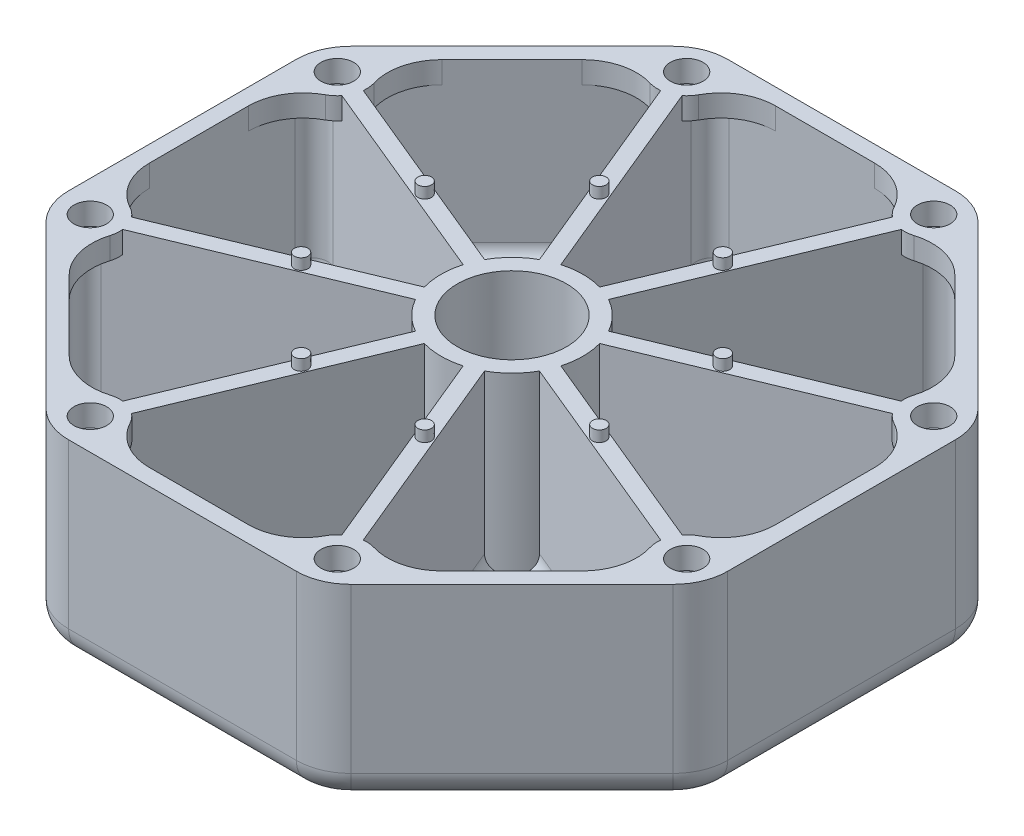
SolidWorks part; units mm, degrees
ref_plane "Front Plane" through (0, 0, 0) normal (0, 0, 1) x (1, 0, 0)
ref_plane "Top Plane" through (0, 0, 0) normal (0, 1, 0) x (1, 0, 0)
ref_plane "Right Plane" through (0, 0, 0) normal (1, 0, 0) x (0, 0, -1)
sketch "Sketch1" plane through (0, 0, 0) normal (0, 1, 0) x (1, 0, 0)
  line L9 (27.9289, -57.4264) -> (57.4264, -27.9289)
  line L10 (60.3553, -20.8579) -> (60.3553, 20.8579)
  line L11 (57.4264, 27.9289) -> (27.9289, 57.4264)
  line L12 (20.8579, 60.3553) -> (-20.8579, 60.3553)
  line L13 (-27.9289, 57.4264) -> (-57.4264, 27.9289)
  line L14 (-60.3553, 20.8579) -> (-60.3553, -20.8579)
  line L15 (-57.4264, -27.9289) -> (-27.9289, -57.4264)
  line L16 (-20.8579, -60.3553) -> (20.8579, -60.3553)
  circle A0 centre (0, 0) radius 60.3553 construction
  arc A9 (-20.8579, 60.3553) -> (-27.9289, 57.4264) centre (-20.8579, 50.3553) ccw
  arc A10 (27.9289, 57.4264) -> (20.8579, 60.3553) centre (20.8579, 50.3553) ccw
  arc A11 (60.3553, 20.8579) -> (57.4264, 27.9289) centre (50.3553, 20.8579) ccw
  arc A12 (57.4264, -27.9289) -> (60.3553, -20.8579) centre (50.3553, -20.8579) ccw
  arc A13 (27.9289, -57.4264) -> (20.8579, -60.3553) centre (20.8579, -50.3553) cw
  arc A14 (-27.9289, -57.4264) -> (-20.8579, -60.3553) centre (-20.8579, -50.3553) ccw
  arc A15 (-60.3553, -20.8579) -> (-57.4264, -27.9289) centre (-50.3553, -20.8579) ccw
  arc A16 (-57.4264, 27.9289) -> (-60.3553, 20.8579) centre (-50.3553, 20.8579) ccw
  point P18 (60.3553, -25)
  point P21 (25, -60.3553)
  dimension "D1" = 50
  dimension "D2" = 10
extrude "Boss-Extrude1" add sketch "Sketch1" along normal blind 3
sketch "Sketch2" plane through (0, 3, 0) normal (0, 1, 0) x (1, 0, 0)
  line L0 (28.0802, -53.0325) -> (53.0325, -28.0802)
  line L1 (57.3553, -17.644) -> (57.3553, 17.644)
  line L2 (53.0325, 28.0802) -> (28.0802, 53.0325)
  line L3 (17.644, 57.3553) -> (-17.644, 57.3553)
  line L4 (-28.0802, 53.0325) -> (-53.0325, 28.0802)
  line L5 (-57.3553, 17.644) -> (-57.3553, -17.644)
  line L6 (-53.0325, -28.0802) -> (-28.0802, -53.0325)
  line L7 (-17.644, -57.3553) -> (17.644, -57.3553)
  line L8 (27.9289, -57.4264) -> (57.4264, -27.9289)
  line L9 (60.3553, -20.8579) -> (60.3553, 20.8579)
  line L10 (57.4264, 27.9289) -> (27.9289, 57.4264)
  line L11 (20.8579, 60.3553) -> (-20.8579, 60.3553)
  line L12 (-27.9289, 57.4264) -> (-57.4264, 27.9289)
  line L13 (-60.3553, 20.8579) -> (-60.3553, -20.8579)
  line L14 (-57.4264, -27.9289) -> (-27.9289, -57.4264)
  line L15 (-20.8579, -60.3553) -> (20.8579, -60.3553)
  line L16 (27.9289, -57.4264) -> (57.4264, -27.9289)
  line L17 (60.3553, -20.8579) -> (60.3553, 20.8579)
  line L18 (57.4264, 27.9289) -> (27.9289, 57.4264)
  line L19 (20.8579, 60.3553) -> (-20.8579, 60.3553)
  line L20 (-27.9289, 57.4264) -> (-57.4264, 27.9289)
  line L21 (-60.3553, 20.8579) -> (-60.3553, -20.8579)
  line L22 (-57.4264, -27.9289) -> (-27.9289, -57.4264)
  line L23 (-20.8579, -60.3553) -> (20.8579, -60.3553)
  line L24 (0, 0) -> (-20.8579, -50.3553) construction
  line L25 (-20.8579, -50.3553) -> (-29.9913, -72.4054) construction
  line L26 (-20.4156, -53.2073) -> (-3.5558, -12.5042)
  line L27 (-23.1872, -52.0592) -> (-6.3275, -11.3562)
  line L28 (-55.3051, -25.8076) -> (-25.8076, -55.3051) construction
  line L29 (-20.8579, -57.3553) -> (20.8579, -57.3553) construction
  line L30 (-52.0592, -23.1872) -> (-11.3562, -6.3275)
  line L31 (-53.2073, -20.4156) -> (-12.5042, -3.5558)
  line L32 (-53.2073, 20.4156) -> (-12.5042, 3.5558)
  line L33 (-52.0592, 23.1872) -> (-11.3562, 6.3275)
  line L34 (-23.1872, 52.0592) -> (-6.3275, 11.3562)
  line L35 (-20.4156, 53.2073) -> (-3.5558, 12.5042)
  line L36 (20.4156, 53.2073) -> (3.5558, 12.5042)
  line L37 (23.1872, 52.0592) -> (6.3275, 11.3562)
  line L38 (52.0592, 23.1872) -> (11.3562, 6.3275)
  line L39 (53.2073, 20.4156) -> (12.5042, 3.5558)
  line L40 (53.2073, -20.4156) -> (12.5042, -3.5558)
  line L41 (52.0592, -23.1872) -> (11.3562, -6.3275)
  line L42 (23.1872, -52.0592) -> (6.3275, -11.3562)
  line L43 (20.4156, -53.2073) -> (3.5558, -12.5042)
  line L44 (-57.3553, 20.8579) -> (-57.3553, -20.8579) construction
  line L45 (-25.8076, 55.3051) -> (-55.3051, 25.8076) construction
  line L46 (20.8579, 57.3553) -> (-20.8579, 57.3553) construction
  line L47 (55.3051, 25.8076) -> (25.8076, 55.3051) construction
  line L48 (57.3553, -20.8579) -> (57.3553, 20.8579) construction
  line L49 (25.8076, -55.3051) -> (55.3051, -25.8076) construction
  arc A8 (57.4264, -27.9289) -> (60.3553, -20.8579) centre (50.3553, -20.8579) ccw
  arc A9 (60.3553, 20.8579) -> (57.4264, 27.9289) centre (50.3553, 20.8579) ccw
  arc A10 (27.9289, 57.4264) -> (20.8579, 60.3553) centre (20.8579, 50.3553) ccw
  arc A11 (-20.8579, 60.3553) -> (-27.9289, 57.4264) centre (-20.8579, 50.3553) ccw
  arc A12 (-57.4264, 27.9289) -> (-60.3553, 20.8579) centre (-50.3553, 20.8579) ccw
  arc A13 (-60.3553, -20.8579) -> (-57.4264, -27.9289) centre (-50.3553, -20.8579) ccw
  arc A14 (-27.9289, -57.4264) -> (-20.8579, -60.3553) centre (-20.8579, -50.3553) ccw
  arc A15 (20.8579, -60.3553) -> (27.9289, -57.4264) centre (20.8579, -50.3553) ccw
  arc A16 (57.4264, -27.9289) -> (60.3553, -20.8579) centre (50.3553, -20.8579) ccw
  arc A17 (60.3553, 20.8579) -> (57.4264, 27.9289) centre (50.3553, 20.8579) ccw
  arc A18 (27.9289, 57.4264) -> (20.8579, 60.3553) centre (20.8579, 50.3553) ccw
  arc A19 (-20.8579, 60.3553) -> (-27.9289, 57.4264) centre (-20.8579, 50.3553) ccw
  arc A20 (-57.4264, 27.9289) -> (-60.3553, 20.8579) centre (-50.3553, 20.8579) ccw
  arc A21 (-60.3553, -20.8579) -> (-57.4264, -27.9289) centre (-50.3553, -20.8579) ccw
  arc A22 (-27.9289, -57.4264) -> (-20.8579, -60.3553) centre (-20.8579, -50.3553) ccw
  arc A23 (20.8579, -60.3553) -> (27.9289, -57.4264) centre (20.8579, -50.3553) ccw
  circle A24 centre (0, 0) radius 10
  arc A25 (-11.3562, -6.3275) -> (-6.3275, -11.3562) centre (0, 0) ccw
  arc A26 (-23.1872, -52.0592) -> (-28.0802, -53.0325) centre (-25.9589, -50.9112) cw
  arc A27 (-17.644, -57.3553) -> (-20.4156, -53.2073) centre (-17.644, -54.3553) cw
  arc A28 (-25.8076, -55.3051) -> (-20.8579, -57.3553) centre (-20.8579, -50.3553) ccw construction
  arc A29 (-53.2073, -20.4156) -> (-57.3553, -17.644) centre (-54.3553, -17.644) cw
  arc A30 (-53.0325, -28.0802) -> (-52.0592, -23.1872) centre (-50.9112, -25.9589) cw
  arc A31 (-52.0592, 23.1872) -> (-53.0325, 28.0802) centre (-50.9112, 25.9589) cw
  arc A32 (-57.3553, 17.644) -> (-53.2073, 20.4156) centre (-54.3553, 17.644) cw
  arc A33 (-20.4156, 53.2073) -> (-17.644, 57.3553) centre (-17.644, 54.3553) cw
  arc A34 (-28.0802, 53.0325) -> (-23.1872, 52.0592) centre (-25.9589, 50.9112) cw
  arc A35 (23.1872, 52.0592) -> (28.0802, 53.0325) centre (25.9589, 50.9112) cw
  arc A36 (17.644, 57.3553) -> (20.4156, 53.2073) centre (17.644, 54.3553) cw
  arc A37 (53.2073, 20.4156) -> (57.3553, 17.644) centre (54.3553, 17.644) cw
  arc A38 (53.0325, 28.0802) -> (52.0592, 23.1872) centre (50.9112, 25.9589) cw
  arc A39 (52.0592, -23.1872) -> (53.0325, -28.0802) centre (50.9112, -25.9589) cw
  arc A40 (57.3553, -17.644) -> (53.2073, -20.4156) centre (54.3553, -17.644) cw
  arc A41 (20.4156, -53.2073) -> (17.644, -57.3553) centre (17.644, -54.3553) cw
  arc A42 (28.0802, -53.0325) -> (23.1872, -52.0592) centre (25.9589, -50.9112) cw
  arc A43 (-57.3553, -20.8579) -> (-55.3051, -25.8076) centre (-50.3553, -20.8579) ccw construction
  arc A44 (-55.3051, 25.8076) -> (-57.3553, 20.8579) centre (-50.3553, 20.8579) ccw construction
  arc A45 (-20.8579, 57.3553) -> (-25.8076, 55.3051) centre (-20.8579, 50.3553) ccw construction
  arc A46 (25.8076, 55.3051) -> (20.8579, 57.3553) centre (20.8579, 50.3553) ccw construction
  arc A47 (57.3553, 20.8579) -> (55.3051, 25.8076) centre (50.3553, 20.8579) ccw construction
  arc A48 (55.3051, -25.8076) -> (57.3553, -20.8579) centre (50.3553, -20.8579) ccw construction
  arc A49 (20.8579, -57.3553) -> (25.8076, -55.3051) centre (20.8579, -50.3553) ccw construction
  circle A50 centre (0, 0) radius 13 construction
  arc A51 (-12.5042, 3.5558) -> (-12.5042, -3.5558) centre (0, 0) ccw
  arc A52 (-6.3275, 11.3562) -> (-11.3562, 6.3275) centre (0, 0) ccw
  arc A53 (3.5558, 12.5042) -> (-3.5558, 12.5042) centre (0, 0) ccw
  arc A54 (11.3562, 6.3275) -> (6.3275, 11.3562) centre (0, 0) ccw
  arc A55 (12.5042, -3.5558) -> (12.5042, 3.5558) centre (0, 0) ccw
  arc A56 (6.3275, -11.3562) -> (11.3562, -6.3275) centre (0, 0) ccw
  arc A57 (-3.5558, -12.5042) -> (3.5558, -12.5042) centre (0, 0) ccw
  point P121 (0, 0)
  dimension "D3" = 20
  dimension "D7" = 3
  dimension "D5" = 1.5
  dimension "D6" = 1.5
  dimension "D1" = 0
  dimension "D2" = 3
  dimension "D4" = 3
extrude "Boss-Extrude2" add sketch "Sketch2" along normal blind 28
sketch "Sketch3" plane through (0, 31, 0) normal (0, 1, 0) x (1, 0, 0)
  line L0 (-20.2449, -52.7952) -> (-20.4156, -53.2073)
  line L1 (50.4221, 19.2619) -> (12.5042, 3.5558)
  line L2 (19.2619, -50.4221) -> (3.5558, -12.5042)
  line L3 (-53.0325, -28.0802) -> (-28.0802, -53.0325)
  line L4 (-23.1872, -52.0592) -> (-6.3275, -11.3562)
  line L5 (-11.3562, -6.3275) -> (-52.0592, -23.1872)
  line L6 (-46.9695, -34.1432) -> (-34.1432, -46.9695)
  line L7 (-22.0336, -49.2741) -> (-6.3275, -11.3562)
  line L8 (-20.8579, -60.3553) -> (20.8579, -60.3553)
  line L9 (27.9289, -57.4264) -> (57.4264, -27.9289)
  line L10 (60.3553, -20.8579) -> (60.3553, 20.8579)
  line L11 (57.4264, 27.9289) -> (27.9289, 57.4264)
  line L12 (20.8579, 60.3553) -> (-20.8579, 60.3553)
  line L13 (-27.9289, 57.4264) -> (-57.4264, 27.9289)
  line L14 (-60.3553, 20.8579) -> (-60.3553, -20.8579)
  line L15 (-57.4264, -27.9289) -> (-27.9289, -57.4264)
  line L16 (-20.8579, -60.3553) -> (20.8579, -60.3553)
  line L17 (27.9289, -57.4264) -> (57.4264, -27.9289)
  line L18 (60.3553, -20.8579) -> (60.3553, 20.8579)
  line L19 (57.4264, 27.9289) -> (27.9289, 57.4264)
  line L20 (20.8579, 60.3553) -> (-20.8579, 60.3553)
  line L21 (-27.9289, 57.4264) -> (-57.4264, 27.9289)
  line L22 (-60.3553, 20.8579) -> (-60.3553, -20.8579)
  line L23 (-57.4264, -27.9289) -> (-27.9289, -57.4264)
  line L24 (-11.3562, -6.3275) -> (-49.2741, -22.0336)
  line L25 (-12.5042, 3.5558) -> (-53.2073, 20.4156)
  line L26 (-53.2073, -20.4156) -> (-12.5042, -3.5558)
  line L27 (-57.3553, 17.644) -> (-57.3553, -17.644)
  line L28 (-12.5042, 3.5558) -> (-50.4221, 19.2619)
  line L30 (-57.3553, 9.0696) -> (-57.3553, -9.0696)
  line L31 (-28.0802, 53.0325) -> (-53.0325, 28.0802)
  line L32 (-52.0592, 23.1872) -> (-11.3562, 6.3275)
  line L33 (-6.3275, 11.3562) -> (-23.1872, 52.0592)
  line L34 (-34.1432, 46.9695) -> (-46.9695, 34.1432)
  line L35 (-49.2741, 22.0336) -> (-11.3562, 6.3275)
  line L36 (-6.3275, 11.3562) -> (-22.0336, 49.2741)
  line L37 (3.5558, 12.5042) -> (20.4156, 53.2073)
  line L38 (-20.4156, 53.2073) -> (-3.5558, 12.5042)
  line L39 (17.644, 57.3553) -> (-17.644, 57.3553)
  line L40 (3.5558, 12.5042) -> (19.2619, 50.4221)
  line L42 (9.0696, 57.3553) -> (-9.0696, 57.3553)
  line L43 (53.0325, 28.0802) -> (28.0802, 53.0325)
  line L44 (23.1872, 52.0592) -> (6.3275, 11.3562)
  line L45 (11.3562, 6.3275) -> (52.0592, 23.1872)
  line L46 (46.9695, 34.1432) -> (34.1432, 46.9695)
  line L48 (11.3562, 6.3275) -> (49.2741, 22.0336)
  line L49 (12.5042, -3.5558) -> (53.2073, -20.4156)
  line L50 (53.2073, 20.4156) -> (12.5042, 3.5558)
  line L51 (57.3553, -17.644) -> (57.3553, 17.644)
  line L52 (12.5042, -3.5558) -> (50.4221, -19.2619)
  line L54 (57.3553, -9.0696) -> (57.3553, 9.0696)
  line L55 (-17.644, -57.3553) -> (17.644, -57.3553)
  line L56 (-3.5558, -12.5042) -> (-20.4156, -53.2073)
  line L57 (20.4156, -53.2073) -> (3.5558, -12.5042)
  line L58 (-9.0696, -57.3553) -> (9.0696, -57.3553)
  line L59 (-3.5558, -12.5042) -> (-19.2619, -50.4221)
  line L61 (28.0802, -53.0325) -> (53.0325, -28.0802)
  line L62 (52.0592, -23.1872) -> (11.3562, -6.3275)
  line L63 (6.3275, -11.3562) -> (23.1872, -52.0592)
  line L64 (34.1432, -46.9695) -> (46.9695, -34.1432)
  line L66 (6.3275, -11.3562) -> (22.0336, -49.2741)
  line L67 (49.2741, -22.0336) -> (11.3562, -6.3275)
  line L68 (22.0336, 49.2741) -> (6.3275, 11.3562)
  line L69 (-19.2619, 50.4221) -> (-3.5558, 12.5042)
  line L70 (-50.4221, -19.2619) -> (-12.5042, -3.5558)
  circle A1 centre (0, 0) radius 10
  circle A2 centre (0, 0) radius 10
  circle A3 centre (-22.6249, -54.6215) radius 3
  arc A5 (-28.0802, -53.0325) -> (-23.1872, -52.0592) centre (-25.9589, -50.9112) ccw
  arc A6 (-11.3562, -6.3275) -> (-6.3275, -11.3562) centre (0, 0) ccw
  arc A7 (-52.0592, -23.1872) -> (-53.0325, -28.0802) centre (-50.9112, -25.9589) ccw
  arc A8 (20.8579, -60.3553) -> (27.9289, -57.4264) centre (20.8579, -50.3553) ccw
  arc A9 (57.4264, -27.9289) -> (60.3553, -20.8579) centre (50.3553, -20.8579) ccw
  arc A10 (60.3553, 20.8579) -> (57.4264, 27.9289) centre (50.3553, 20.8579) ccw
  arc A11 (27.9289, 57.4264) -> (20.8579, 60.3553) centre (20.8579, 50.3553) ccw
  arc A12 (-20.8579, 60.3553) -> (-27.9289, 57.4264) centre (-20.8579, 50.3553) ccw
  arc A13 (-57.4264, 27.9289) -> (-60.3553, 20.8579) centre (-50.3553, 20.8579) ccw
  arc A14 (-60.3553, -20.8579) -> (-57.4264, -27.9289) centre (-50.3553, -20.8579) ccw
  arc A15 (-27.9289, -57.4264) -> (-20.8579, -60.3553) centre (-20.8579, -50.3553) ccw
  arc A16 (20.8579, -60.3553) -> (27.9289, -57.4264) centre (20.8579, -50.3553) ccw
  arc A17 (57.4264, -27.9289) -> (60.3553, -20.8579) centre (50.3553, -20.8579) ccw
  arc A18 (60.3553, 20.8579) -> (57.4264, 27.9289) centre (50.3553, 20.8579) ccw
  arc A19 (27.9289, 57.4264) -> (20.8579, 60.3553) centre (20.8579, 50.3553) ccw
  arc A20 (-20.8579, 60.3553) -> (-27.9289, 57.4264) centre (-20.8579, 50.3553) ccw
  arc A21 (-57.4264, 27.9289) -> (-60.3553, 20.8579) centre (-50.3553, 20.8579) ccw
  arc A22 (-60.3553, -20.8579) -> (-57.4264, -27.9289) centre (-50.3553, -20.8579) ccw
  arc A23 (-27.9289, -57.4264) -> (-20.8579, -60.3553) centre (-20.8579, -50.3553) ccw
  arc A25 (-11.3562, -6.3275) -> (-6.3275, -11.3562) centre (0, 0) ccw
  arc A27 (-12.5042, 3.5558) -> (-12.5042, -3.5558) centre (0, 0) ccw
  arc A28 (-57.3553, -17.644) -> (-53.2073, -20.4156) centre (-54.3553, -17.644) ccw
  arc A29 (-53.2073, 20.4156) -> (-57.3553, 17.644) centre (-54.3553, 17.644) ccw
  arc A30 (-12.5042, 3.5558) -> (-12.5042, -3.5558) centre (0, 0) ccw
  arc A33 (-53.0325, 28.0802) -> (-52.0592, 23.1872) centre (-50.9112, 25.9589) ccw
  arc A34 (-6.3275, 11.3562) -> (-11.3562, 6.3275) centre (0, 0) ccw
  arc A35 (-23.1872, 52.0592) -> (-28.0802, 53.0325) centre (-25.9589, 50.9112) ccw
  arc A37 (-6.3275, 11.3562) -> (-11.3562, 6.3275) centre (0, 0) ccw
  arc A39 (3.5558, 12.5042) -> (-3.5558, 12.5042) centre (0, 0) ccw
  arc A40 (-17.644, 57.3553) -> (-20.4156, 53.2073) centre (-17.644, 54.3553) ccw
  arc A41 (20.4156, 53.2073) -> (17.644, 57.3553) centre (17.644, 54.3553) ccw
  arc A42 (3.5558, 12.5042) -> (-3.5558, 12.5042) centre (0, 0) ccw
  arc A45 (28.0802, 53.0325) -> (23.1872, 52.0592) centre (25.9589, 50.9112) ccw
  arc A46 (11.3562, 6.3275) -> (6.3275, 11.3562) centre (0, 0) ccw
  arc A47 (52.0592, 23.1872) -> (53.0325, 28.0802) centre (50.9112, 25.9589) ccw
  arc A49 (11.3562, 6.3275) -> (6.3275, 11.3562) centre (0, 0) ccw
  arc A51 (12.5042, -3.5558) -> (12.5042, 3.5558) centre (0, 0) ccw
  arc A52 (57.3553, 17.644) -> (53.2073, 20.4156) centre (54.3553, 17.644) ccw
  arc A53 (53.2073, -20.4156) -> (57.3553, -17.644) centre (54.3553, -17.644) ccw
  arc A54 (12.5042, -3.5558) -> (12.5042, 3.5558) centre (0, 0) ccw
  arc A57 (-20.4156, -53.2073) -> (-17.644, -57.3553) centre (-17.644, -54.3553) ccw
  arc A58 (-3.5558, -12.5042) -> (3.5558, -12.5042) centre (0, 0) ccw
  arc A59 (17.644, -57.3553) -> (20.4156, -53.2073) centre (17.644, -54.3553) ccw
  arc A61 (-3.5558, -12.5042) -> (3.5558, -12.5042) centre (0, 0) ccw
  arc A63 (53.0325, -28.0802) -> (52.0592, -23.1872) centre (50.9112, -25.9589) ccw
  arc A64 (6.3275, -11.3562) -> (11.3562, -6.3275) centre (0, 0) ccw
  arc A65 (23.1872, -52.0592) -> (28.0802, -53.0325) centre (25.9589, -50.9112) ccw
  arc A67 (6.3275, -11.3562) -> (11.3562, -6.3275) centre (0, 0) ccw
  arc A75 (-17.8832, -52.0797) -> (-19.2619, -50.4221) centre (-22.6249, -54.6215) ccw
  circle A83 centre (-22.6249, -54.6215) radius 5.38 construction
  arc A84 (-34.1432, -46.9695) -> (-24.1806, -49.4713) centre (-27.0721, -39.8984) ccw
  arc A85 (-9.0696, -57.3553) -> (-17.8832, -52.0797) centre (-9.0696, -47.3553) cw
  arc A86 (-46.9695, -34.1432) -> (-49.4713, -24.1806) centre (-39.8984, -27.0721) cw
  arc A87 (-49.4713, -24.1806) -> (-49.2741, -22.0336) centre (-54.6215, -22.6249) ccw
  arc A88 (-57.3553, -9.0696) -> (-52.0797, -17.8832) centre (-47.3553, -9.0696) ccw
  circle A89 centre (-54.6215, -22.6249) radius 3
  arc A90 (-57.3553, 9.0696) -> (-52.0797, 17.8832) centre (-47.3553, 9.0696) cw
  arc A91 (-52.0797, 17.8832) -> (-50.4221, 19.2619) centre (-54.6215, 22.6249) ccw
  arc A92 (-46.9695, 34.1432) -> (-49.4713, 24.1806) centre (-39.8984, 27.0721) ccw
  circle A93 centre (-54.6215, 22.6249) radius 3
  arc A94 (-34.1432, 46.9695) -> (-24.1806, 49.4713) centre (-27.0721, 39.8984) cw
  arc A95 (-24.1806, 49.4713) -> (-22.0336, 49.2741) centre (-22.6249, 54.6215) ccw
  arc A96 (-9.0696, 57.3553) -> (-17.8832, 52.0797) centre (-9.0696, 47.3553) ccw
  circle A97 centre (-22.6249, 54.6215) radius 3
  arc A98 (9.0696, 57.3553) -> (17.8832, 52.0797) centre (9.0696, 47.3553) cw
  arc A99 (17.8832, 52.0797) -> (19.2619, 50.4221) centre (22.6249, 54.6215) ccw
  arc A100 (34.1432, 46.9695) -> (24.1806, 49.4713) centre (27.0721, 39.8984) ccw
  circle A101 centre (22.6249, 54.6215) radius 3
  arc A102 (46.9695, 34.1432) -> (49.4713, 24.1806) centre (39.8984, 27.0721) cw
  arc A103 (49.4713, 24.1806) -> (49.2741, 22.0336) centre (54.6215, 22.6249) ccw
  arc A104 (57.3553, 9.0696) -> (52.0797, 17.8832) centre (47.3553, 9.0696) ccw
  circle A105 centre (54.6215, 22.6249) radius 3
  arc A106 (57.3553, -9.0696) -> (52.0797, -17.8832) centre (47.3553, -9.0696) cw
  arc A107 (52.0797, -17.8832) -> (50.4221, -19.2619) centre (54.6215, -22.6249) ccw
  arc A108 (46.9695, -34.1432) -> (49.4713, -24.1806) centre (39.8984, -27.0721) ccw
  circle A109 centre (54.6215, -22.6249) radius 3
  arc A110 (34.1432, -46.9695) -> (24.1806, -49.4713) centre (27.0721, -39.8984) cw
  arc A111 (24.1806, -49.4713) -> (22.0336, -49.2741) centre (22.6249, -54.6215) ccw
  arc A112 (9.0696, -57.3553) -> (17.8832, -52.0797) centre (9.0696, -47.3553) ccw
  circle A113 centre (22.6249, -54.6215) radius 3
  arc A114 (22.0336, 49.2741) -> (24.1806, 49.4713) centre (22.6249, 54.6215) ccw
  arc A115 (50.4221, 19.2619) -> (52.0797, 17.8832) centre (54.6215, 22.6249) ccw
  arc A116 (49.2741, -22.0336) -> (49.4713, -24.1806) centre (54.6215, -22.6249) ccw
  arc A117 (19.2619, -50.4221) -> (17.8832, -52.0797) centre (22.6249, -54.6215) ccw
  arc A118 (-22.0336, -49.2741) -> (-24.1806, -49.4713) centre (-22.6249, -54.6215) ccw
  arc A119 (-50.4221, -19.2619) -> (-52.0797, -17.8832) centre (-54.6215, -22.6249) ccw
  arc A120 (-49.2741, 22.0336) -> (-49.4713, 24.1806) centre (-54.6215, 22.6249) ccw
  arc A121 (-19.2619, 50.4221) -> (-17.8832, 52.0797) centre (-22.6249, 54.6215) ccw
  point P92 (-22.6249, -54.6215)
  point P116 (0, 0)
  point P180 (0, 0)
  dimension "D11" = 6
  dimension "D13" = 10
  dimension "D1" = 0
  dimension "D2" = 0
  dimension "D3" = 0
  dimension "D4" = 0
  dimension "D5" = 0
  dimension "D6" = 0
  dimension "D7" = 0
  dimension "D8" = 0
  dimension "D9" = 0
  dimension "D10" = 0
  dimension "D12" = 2.38
  dimension "D14" = 8
extrude "Boss-Extrude3" add sketch "Sketch3" along normal blind 4 contours L23 A23 L16 A16 L17 A17 L18 A18 L19 A19 L20 A20 L21 A21 L22 A22 A113 A112 L58 A85 A75 A84 L6 A86 A87 A88 L30 A90 A91 A92 L34 A94 A95 A96 L42 A98 A99 A100 L46
sketch "Sketch4" plane through (0, 35, 0) normal (0, 1, 0) x (1, 0, 0)
  line L0 (0, 0) -> (22.6249, -54.6215) construction
  circle A0 centre (0, 0) radius 52.5 construction
  circle A1 centre (11.3125, -27.3107) radius 1.25
  circle A2 centre (-11.3125, -27.3107) radius 1.25
  circle A3 centre (-27.3107, -11.3125) radius 1.25
  circle A4 centre (-27.3107, 11.3125) radius 1.25
  circle A5 centre (-11.3125, 27.3107) radius 1.25
  circle A6 centre (11.3125, 27.3107) radius 1.25
  circle A7 centre (27.3107, 11.3125) radius 1.25
  circle A8 centre (27.3107, -11.3125) radius 1.25
  point P3 (22.6249, -54.6215)
  point P24 (0, 0)
  dimension "D1" = 105
  dimension "D2" = 2.5
  dimension "D3" = 8
extrude "Boss-Extrude4" add sketch "Sketch4" along normal blind 2
fillet "Fillet1" radius 5 16 edges at (-24.6847, 0, -59.5941) (0, 0, -60.3553) (24.6847, 0, -59.5941) (42.6777, 0, -42.6777) (59.5941, 0, -24.6847) (60.3553, 0, 0) (59.5941, 0, 24.6847) (42.6777, 0, 42.6777) (24.6847, 0, 59.5941) (0, 0, 60.3553) (-24.6847, 0, 59.5941) (-42.6777, 0, 42.6777) (-59.5941, 0, 24.6847) (-60.3553, 0, 0) (-59.5941, 0, -24.6847) (-42.6777, 0, -42.6777)
fillet "Fillet3" radius 3 40 edges at (-32.8558, 3, 11.9857) (-56.022, 3, 20.1384) (-57.3553, 3, 0) (-56.022, 3, -20.1384) (-31.7077, 3, 14.7574) (-53.8535, 3, 25.3736) (-40.5563, 3, 40.5563) (-25.3736, 3, 53.8535) (-11.9857, 3, 32.8558) (-20.1384, 3, 56.022) (0, 3, 57.3553) (20.1384, 3, 56.022) (14.7574, 3, 31.7077) (25.3736, 3, 53.8535) (31.7077, 3, 14.7574) (53.8535, 3, 25.3736) (32.8558, 3, 11.9857) (56.022, 3, 20.1384) (32.8558, 3, -11.9857) (56.022, 3, -20.1384) (-31.7077, 3, -14.7574) (-53.8535, 3, -25.3736) (-40.5563, 3, -40.5563) (-25.3736, 3, -53.8535) (11.9857, 3, -32.8558) (20.1384, 3, -56.022) (-11.9857, 3, -32.8558) (-20.1384, 3, -56.022) (31.7077, 3, -14.7574) (53.8535, 3, -25.3736) (14.7574, 3, -31.7077) (25.3736, 3, -53.8535) (-32.8558, 3, -11.9857) (-14.7574, 3, 31.7077) (11.9857, 3, 32.8558) (40.5563, 3, 40.5563) (57.3553, 3, 0) (-14.7574, 3, -31.7077) (0, 3, -57.3553) (40.5563, 3, -40.5563)
